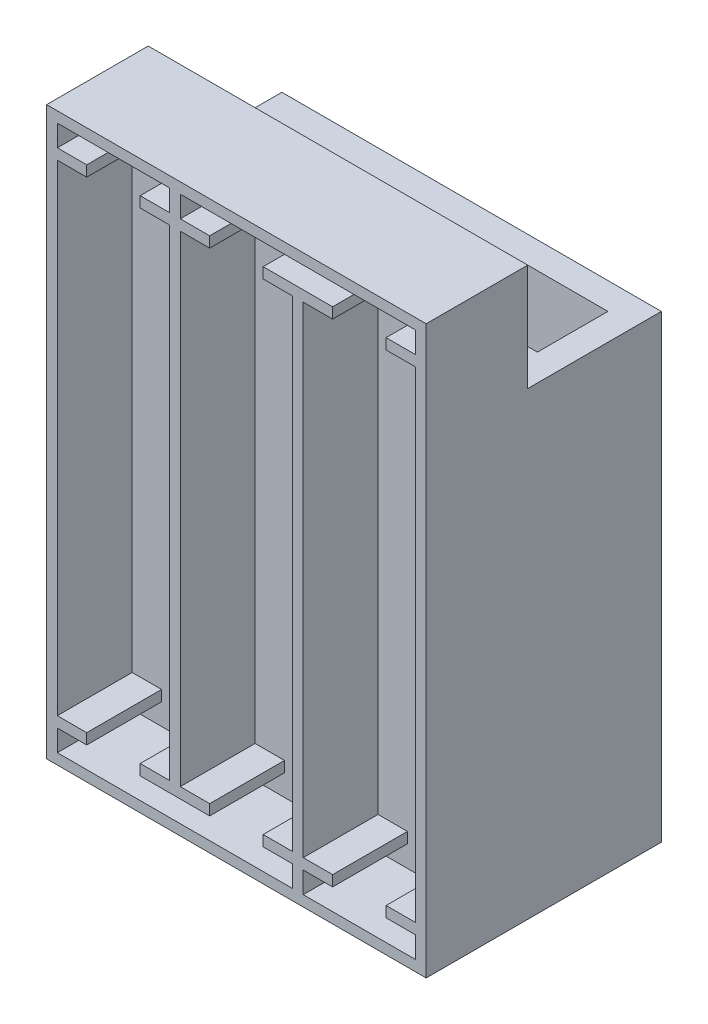
SolidWorks part; units mm, degrees
ref_plane "Front Plane" through (0, 0, 0) normal (0, 0, 1) x (1, 0, 0)
ref_plane "Top Plane" through (0, 0, 0) normal (0, 1, 0) x (1, 0, 0)
ref_plane "Right Plane" through (0, 0, 0) normal (1, 0, 0) x (0, 0, -1)
sketch "Sketch1" plane through (0, 0, 0) normal (0, 1, 0) x (1, 0, 0)
  line L1 (-15.25, -5) -> (15.25, -5)
  line L2 (-15.25, -5) -> (-15.25, 5)
  line L3 (-15.25, 5) -> (15.25, 5)
  line L4 (15.25, -5) -> (15.25, 5)
  line L5 (-15.25, -5) -> (15.25, 5) construction
  line L6 (-15.25, 5) -> (15.25, -5) construction
  point P0 (0, 0)
  dimension "D1" = 30.5
  dimension "D2" = 10
extrude "Boss-Extrude1" add sketch "Sketch1" along normal blind 2.5
sketch "Sketch2" plane through (0, 0, 0) normal (0, 1, 0) x (1, 0, 0)
  line L0 (15.25, 5) -> (-15.25, 5) construction
  line L1 (-17.75, -7.5) -> (17.75, -7.5)
  line L2 (-17.75, -7.5) -> (-17.75, 7.5)
  line L3 (-17.75, 7.5) -> (17.75, 7.5)
  line L4 (17.75, -7.5) -> (17.75, 7.5)
  line L5 (-17.75, -7.5) -> (17.75, 7.5) construction
  line L6 (-17.75, 7.5) -> (17.75, -7.5) construction
  line L7 (-15.25, 5) -> (-15.25, -5) construction
  line L8 (-15.25, 5) -> (-15.25, -5)
  line L9 (-15.25, -5) -> (-10.25, -5)
  line L10 (-15.25, -5) -> (15.25, -5) construction
  line L11 (-10.25, -5) -> (-10.25, -1.6)
  line L12 (-10.25, -1.6) -> (15.25, -1.6)
  line L13 (15.25, -5) -> (15.25, 5) construction
  line L14 (15.25, -1.6) -> (15.25, 5)
  line L15 (15.25, 5) -> (-15.25, 5)
  point P0 (0, 0)
  dimension "D1" = 2.5
  dimension "D2" = 2.5
  dimension "D3" = 6.6
  dimension "D4" = 5
extrude "Boss-Extrude3" add sketch "Sketch2" along normal blind 43
sketch "Sketch3" plane through (0, 43, 0) normal (0, 1, 0) x (1, 0, 0)
  line L0 (-10.25, -5) -> (-3.25, -5)
  line L1 (-3.25, -5) -> (-3.25, -1.6)
  line L2 (-10.25, -1.6) -> (15.25, -1.6) construction
  line L3 (-3.25, -1.6) -> (-10.25, -1.6)
  line L4 (-10.25, -1.6) -> (-10.25, -5)
  dimension "D1" = 7
extrude "Cut-Extrude1" cut sketch "Sketch3" against normal blind 29
sketch "Sketch4" plane through (0, 43, 0) normal (0, 1, 0) x (1, 0, 0)
  line L0 (-15.25, -5) -> (-17.75, -5) construction
  line L1 (-17.75, 7.5) -> (-17.75, -7.5) construction
  line L3 (17.75, -7.5) -> (-17.75, -7.5)
  line L4 (17.75, -7.5) -> (17.75, -5)
  line L5 (17.75, -5) -> (-17.75, -5)
  line L6 (-17.75, -7.5) -> (-17.75, -5)
extrude "Boss-Extrude4" add sketch "Sketch4" along normal blind 10
sketch "Sketch5" plane through (0, 0, 7.5) normal (0, 0, 1) x (1, 0, 0)
  line L5 (-17.75, 26.5) -> (17.75, 26.5) construction
  line L11 (-17.75, 53) -> (-17.75, 0) construction
  line L20 (17.75, 53) -> (17.75, 0) construction
  line L21 (-17.75, 0) -> (-17.75, 53)
  line L22 (-17.75, 53) -> (17.75, 53)
  line L23 (17.75, 53) -> (17.75, 0)
  line L24 (-16.75, 1) -> (-16.75, 52)
  line L25 (-16.75, 52) -> (16.75, 52)
  line L26 (16.75, 52) -> (16.75, 1)
  line L27 (-17.75, 0) -> (17.75, 0)
  line L28 (-16.75, 1) -> (16.75, 1)
  point P16 (16.75, 26.5)
  point P17 (-16.75, 26.5)
  dimension "D1" = 1
  dimension "D2" = 1
  dimension "D3" = 1
extrude "Boss-Extrude5" add sketch "Sketch5" along normal blind 7
sketch "Sketch6" plane through (0, 0, 7.5) normal (0, 0, 1) x (1, 0, 0)
  line L0 (-6.25, 52) -> (-6.25, 50)
  line L1 (16.75, 52) -> (-16.75, 52) construction
  line L2 (-16.75, 1) -> (16.75, 1) construction
  line L3 (-6.25, 1) -> (-5.25, 1)
  line L4 (-5.25, 1) -> (-5.25, 3)
  line L5 (-5.25, 52) -> (-6.25, 52)
  line L6 (-16.75, 52) -> (-16.75, 1) construction
  line L7 (6.25, 52) -> (5.25, 52)
  line L8 (5.25, 52) -> (5.25, 50)
  line L9 (5.25, 1) -> (6.25, 1)
  line L10 (6.25, 1) -> (6.25, 3)
  line L13 (16.75, 1) -> (16.75, 52) construction
  line L14 (-16.75, 50) -> (-6.25, 50)
  line L15 (-16.75, 50) -> (-16.75, 49)
  line L16 (-16.75, 49) -> (-6.25, 49)
  line L17 (16.75, 50) -> (16.75, 49)
  line L18 (16.75, 52) -> (-16.75, 52) construction
  line L19 (-16.75, 26.5) -> (16.75, 26.5) construction
  line L20 (-16.75, 52) -> (-16.75, 1) construction
  line L21 (-16.75, 4) -> (-6.25, 4)
  line L22 (16.75, 3) -> (16.75, 4)
  line L23 (-16.75, 3) -> (-6.25, 3)
  line L24 (-16.75, 3) -> (-16.75, 4)
  line L25 (-6.25, 49) -> (-6.25, 4)
  line L26 (-5.25, 50) -> (-5.25, 52)
  line L27 (-5.25, 50) -> (5.25, 50)
  line L28 (-5.25, 49) -> (5.25, 49)
  line L29 (6.25, 50) -> (6.25, 52)
  line L30 (5.25, 49) -> (5.25, 4)
  line L31 (6.25, 50) -> (16.75, 50)
  line L32 (6.25, 49) -> (16.75, 49)
  line L33 (-5.25, 3) -> (5.25, 3)
  line L34 (-5.25, 4) -> (5.25, 4)
  line L35 (-6.25, 3) -> (-6.25, 1)
  line L36 (-5.25, 4) -> (-5.25, 49)
  line L37 (6.25, 3) -> (16.75, 3)
  line L38 (6.25, 4) -> (16.75, 4)
  line L39 (5.25, 3) -> (5.25, 1)
  line L40 (6.25, 4) -> (6.25, 49)
  dimension "D1" = 1
  dimension "D2" = 10.5
  dimension "D4" = 10.5
  dimension "D5" = 1
  dimension "D6" = 2
  dimension "D3" = 2
extrude "Boss-Extrude6" add sketch "Sketch6" along normal blind 7
sketch "Sketch7" plane through (0, 0, 14.5) normal (0, 0, 1) x (1, 0, 0)
  line L0 (-16.75, 26.5) -> (16.75, 26.5) construction
  line L1 (-16.75, 49) -> (-16.75, 4) construction
  line L2 (16.75, 4) -> (16.75, 49) construction
  line L3 (-11.5, 50) -> (-11.5, 49) construction
  line L6 (-6.25, 50) -> (-16.75, 50) construction
  line L9 (-16.75, 49) -> (-6.25, 49) construction
  line L12 (-2.5, 49) -> (-2.5, 50)
  line L13 (-14, 49) -> (-9, 49)
  line L14 (-14, 49) -> (-14, 50)
  line L15 (-14, 50) -> (-9, 50)
  line L16 (-9, 49) -> (-9, 50)
  line L17 (-14, 49) -> (-9, 50) construction
  line L18 (-14, 50) -> (-9, 49) construction
  line L19 (-2.5, 49) -> (2.5, 49)
  line L20 (2.5, 49) -> (2.5, 50)
  line L21 (-2.5, 50) -> (2.5, 50)
  line L22 (9, 49) -> (9, 50)
  line L23 (9, 49) -> (14, 49)
  line L24 (14, 49) -> (14, 50)
  line L25 (9, 50) -> (14, 50)
  line L28 (9, 4) -> (14, 4)
  line L29 (5.25, 52) -> (6.25, 52)
  line L30 (5.25, 52) -> (5.25, 50)
  line L31 (5.25, 50) -> (6.25, 50)
  line L32 (6.25, 52) -> (6.25, 50)
  line L33 (14, 4) -> (14, 3)
  line L34 (9, 3) -> (14, 3)
  line L35 (9, 4) -> (9, 3)
  line L36 (-2.5, 4) -> (2.5, 4)
  line L37 (2.5, 4) -> (2.5, 3)
  line L38 (-2.5, 3) -> (2.5, 3)
  line L39 (-2.5, 4) -> (-2.5, 3)
  line L40 (-14, 3) -> (-9, 3)
  line L41 (-9, 4) -> (-9, 3)
  line L42 (-14, 4) -> (-9, 4)
  line L43 (-14, 4) -> (-14, 3)
  line L45 (-6.25, 3) -> (-5.25, 3)
  line L46 (-6.25, 3) -> (-6.25, 1)
  line L47 (-6.25, 1) -> (-5.25, 1)
  line L48 (-5.25, 3) -> (-5.25, 1)
  point P12 (-11.5, 49.5)
  dimension "D1" = 5
  dimension "D3" = 6.5
  dimension "D2" = 3
extrude "Cut-Extrude2" cut sketch "Sketch7" against normal up to surface (7 mm away) up to face at (-11.5, 26.5, 7.5)
sketch "Sketch8" plane through (0, 0, 7.5) normal (0, 0, 1) x (1, 0, 0)
  line L0 (11.5, 1) -> (11.5, 52) construction
  line L3 (6.25, 1) -> (16.75, 1) construction
  line L8 (16.75, 52) -> (-5.25, 52) construction
  line L10 (10.7, 45) -> (12.3, 45)
  line L11 (10.7, 45) -> (10.7, 1)
  line L12 (10.7, 1) -> (12.3, 1)
  line L13 (12.3, 45) -> (12.3, 1)
  line L14 (10.7, 45) -> (12.3, 1) construction
  line L15 (10.7, 1) -> (12.3, 45) construction
  point P6 (11.5, 23)
  dimension "D1" = 1.6
  dimension "D2" = 7
extrude "Cut-Extrude3" cut sketch "Sketch8" against normal blind 2.5
